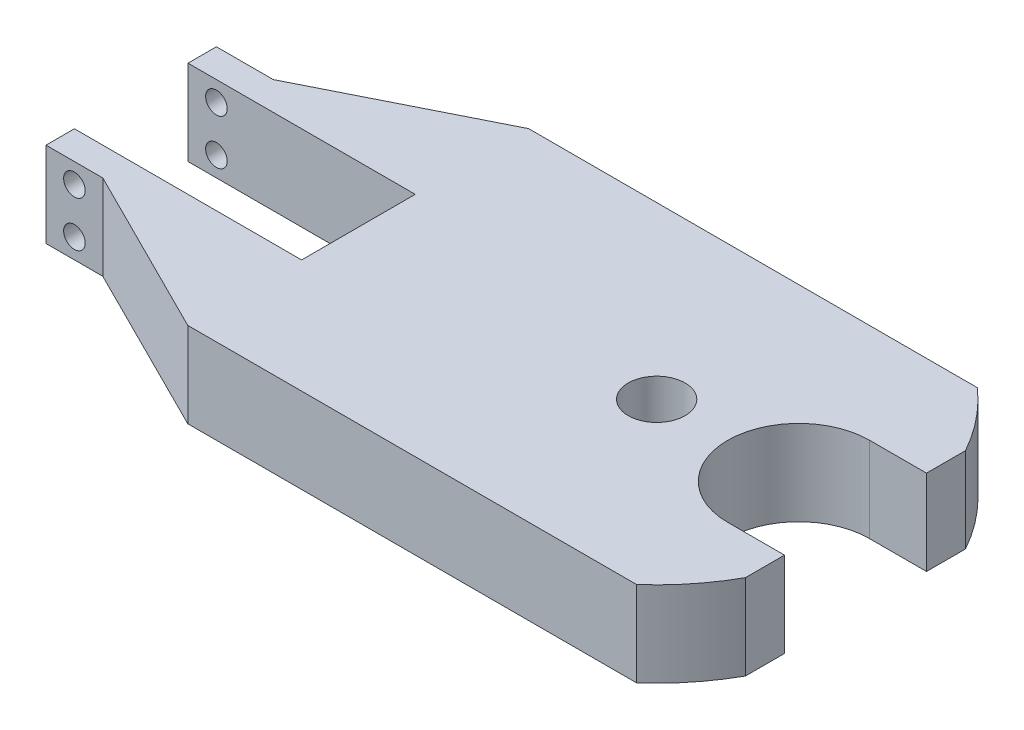
SolidWorks part; units mm, degrees
ref_plane "Front Plane" through (0, 0, 0) normal (0, 0, 1) x (1, 0, 0)
ref_plane "Top Plane" through (0, 0, 0) normal (0, 1, 0) x (1, 0, 0)
ref_plane "Right Plane" through (0, 0, 0) normal (1, 0, 0) x (0, 0, -1)
sketch "Sketch1" plane through (0, 0, 0) normal (0, 1, 0) x (1, 0, 0)
  line L0 (-5.729, 0) -> (9.3381, 0) construction
  line L1 (0, 1) -> (-4, 1)
  line L2 (-4, 1) -> (-4, 1.5)
  line L3 (-4, 1.5) -> (-3, 1.5)
  line L4 (-3, 1.5) -> (-0.0046, 3)
  line L5 (-0.0046, 3) -> (7.8958, 3)
  line L6 (8.75, 1.9365) -> (8.75, 1.25)
  line L7 (8.75, 1.25) -> (7.75, 1.25)
  line L8 (8.75, -1.9365) -> (8.75, -1.25)
  line L9 (0, 1) -> (0, -1)
  line L10 (8.75, -1.25) -> (7.75, -1.25)
  line L11 (-4, -1) -> (-4, -1.5)
  line L12 (-4, -1.5) -> (-3, -1.5)
  line L13 (0, -1) -> (-4, -1)
  line L14 (-3, -1.5) -> (-0.0046, -3)
  line L15 (-0.0046, -3) -> (7.8958, -3)
  arc A0 (7.75, 1.25) -> (7.75, -1.25) centre (7.75, 0) ccw
  circle A1 centre (5.25, 0) radius 0.5
  arc A2 (8.75, 1.9365) -> (7.8958, 3) centre (5.25, 0) ccw
  arc A3 (8.75, -1.9365) -> (7.8958, -3) centre (5.25, 0) cw
  point P24 (0, 0)
  dimension "D10" = 2.5
  dimension "D12" = 4
  dimension "D13" = 1
  dimension "D1" = 4
  dimension "D2" = 1
  dimension "D3" = 1.5
  dimension "D4" = 12.75
  dimension "D5" = 0.5
  dimension "D6" = 3.35
  dimension "D7" = 1
  dimension "D8" = 3
  dimension "D9" = 1
  dimension "D11" = 2.5
extrude "Boss-Extrude1" add sketch "Sketch1" along normal mid plane 1.5
sketch "Sketch2" plane through (0, 0, 1.5) normal (0, 0, 1) x (1, 0, 0)
  line L0 (-4, 0.75) -> (-4, -0.75) construction
  line L1 (-4, 0.75) -> (-3, 0.75) construction
  line L2 (-4, -0.75) -> (-3, -0.75) construction
  circle A0 centre (-3.5, 0.4) radius 0.19
  circle A1 centre (-3.5, -0.4) radius 0.19
  point P10 (0, 0)
  dimension "D1" = 0.38
  dimension "D2" = 0.5
  dimension "D3" = 0.5
  dimension "D4" = 0.35
  dimension "D5" = 0.35
extrude "Cut-Extrude1" cut sketch "Sketch2" against normal through all
sketch "Sketch3" plane through (0, 0, 0) normal (-1, 0, 0) x (0, 0, 1)
  line L0 (-1, -0.75) -> (1, -0.75) construction
  circle A0 centre (0, 0) radius 0.375
  dimension "D1" = 0.75
  dimension "D2" = 0.75
extrude "Cut-Extrude2" cut sketch "Sketch3" against normal blind 0.75
